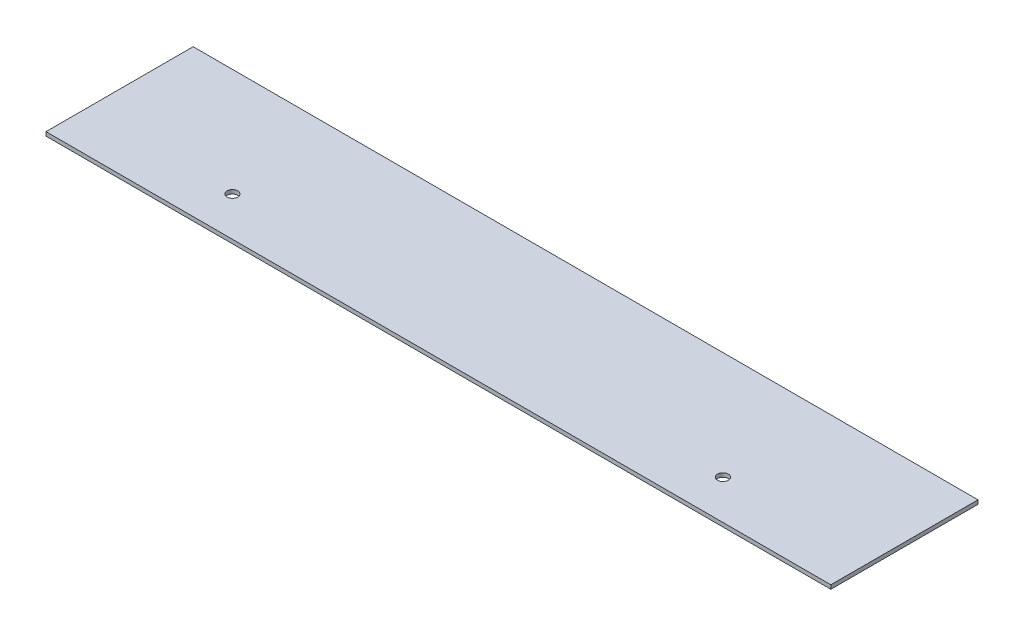
SolidWorks part; units mm, degrees
ref_plane "Front Plane" through (0, 0, 0) normal (0, 0, 1) x (1, 0, 0)
ref_plane "Top Plane" through (0, 0, 0) normal (0, 1, 0) x (1, 0, 0)
ref_plane "Right Plane" through (0, 0, 0) normal (1, 0, 0) x (0, 0, -1)
sketch "Sketch1" plane through (0, 0, 0) normal (0, 1, 0) x (1, 0, 0)
  line L1 (0, 0) -> (160, 0)
  line L2 (0, 0) -> (0, 30)
  line L3 (0, 30) -> (160, 30)
  line L4 (160, 0) -> (160, 30)
  circle A0 centre (30, 8) radius 1.1
  circle A1 centre (130, 8) radius 1.1
  point P9 (80, 0)
  point P10 (0, 15)
  point P11 (0, 0)
  point P12 (0, 0)
  point P13 (0, 0)
  dimension "D3" = 7
  dimension "D5" = 2.2
  dimension "D1" = 30
  dimension "D2" = 160
  dimension "D4" = 50
  dimension "D6" = 50
extrude "Boss-Extrude1" add sketch "Sketch1" along normal blind 0.8
